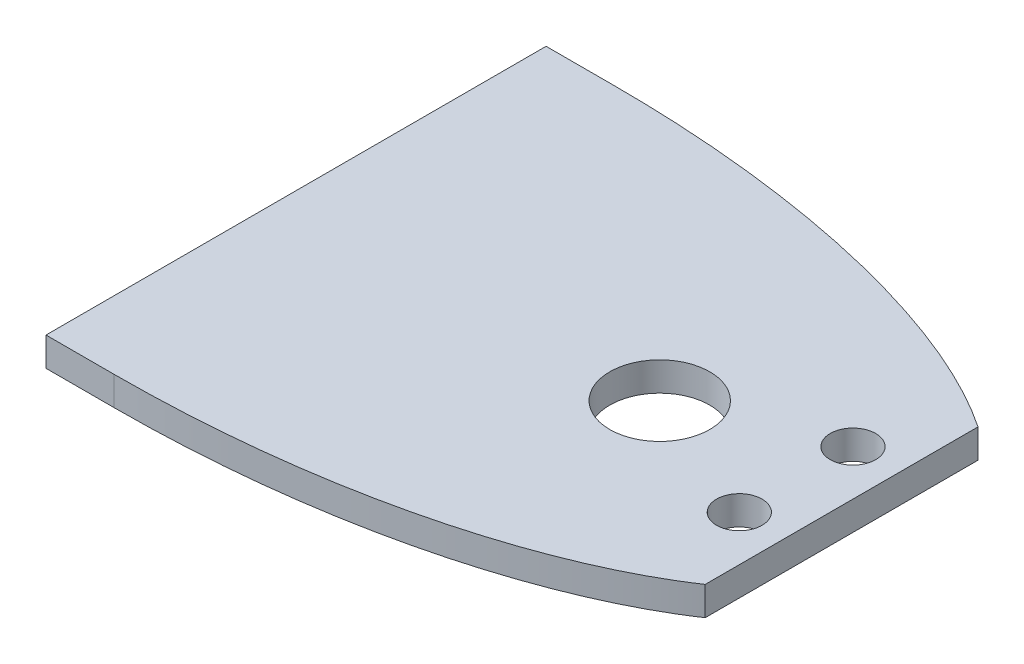
SolidWorks part; units mm, degrees
ref_plane "Front Plane" through (0, 0, 0) normal (0, 0, 1) x (1, 0, 0)
ref_plane "Top Plane" through (0, 0, 0) normal (0, 1, 0) x (1, 0, 0)
ref_plane "Right Plane" through (0, 0, 0) normal (1, 0, 0) x (0, 0, -1)
sketch "Sketch1" plane through (0, 0, 0) normal (0, 1, 0) x (1, 0, 0)
  line L1 (0, 110) -> (0, 0)
  line L2 (105, 85) -> (105, 25)
  ellipse E0 centre (0, 55) end of major axis (-125.2773, 55) minor radius 55 (105, 85) -> (0, 110) ccw
  ellipse E1 centre (0, 55) end of major axis (-125.2773, 55) minor radius 55 (0, 0) -> (105, 25) ccw
  dimension "D1" = 110
  dimension "D2" = 60
  dimension "D3" = 105
extrude "Boss-Extrude1" add sketch "Sketch1" along normal blind 6.35
sketch "Sketch2" plane through (0, 0, 0) normal (0, 1, 0) x (1, 0, 0)
  circle A0 centre (95, 67.5) radius 5
  circle A1 centre (95, 42.5) radius 5
  dimension "D1" = 10
  dimension "D4" = 10
  dimension "D2" = 17.5
  dimension "D3" = 42.5
extrude "Cut-Extrude1" cut sketch "Sketch2" along normal blind 6.35
sketch "Sketch3" plane through (0, 0, 0) normal (0, 1, 0) x (1, 0, 0)
  circle A0 centre (65, 55) radius 11
  dimension "D2" = 22
  dimension "D1" = 30
  dimension "D3" = 40
extrude "Cut-Extrude2" cut sketch "Sketch3" along normal through all
sketch "Sketch4" plane through (0, 0, 0) normal (0, 1, 0) x (1, 0, 0)
  line L0 (0, 110) -> (-15, 110)
  line L1 (0, 110) -> (0, 0) construction
  line L2 (-15, 110) -> (-15, 0)
  line L3 (-15, 0) -> (0, 0)
  line L4 (0, 0) -> (0, 110)
  ellipse E0 centre (0, 55) end of major axis (-125.2773, 55) minor radius 55 (105, 85) -> (0, 110) ccw construction
  dimension "D1" = 15
extrude "Boss-Extrude3" add sketch "Sketch4" along normal blind 6.35
